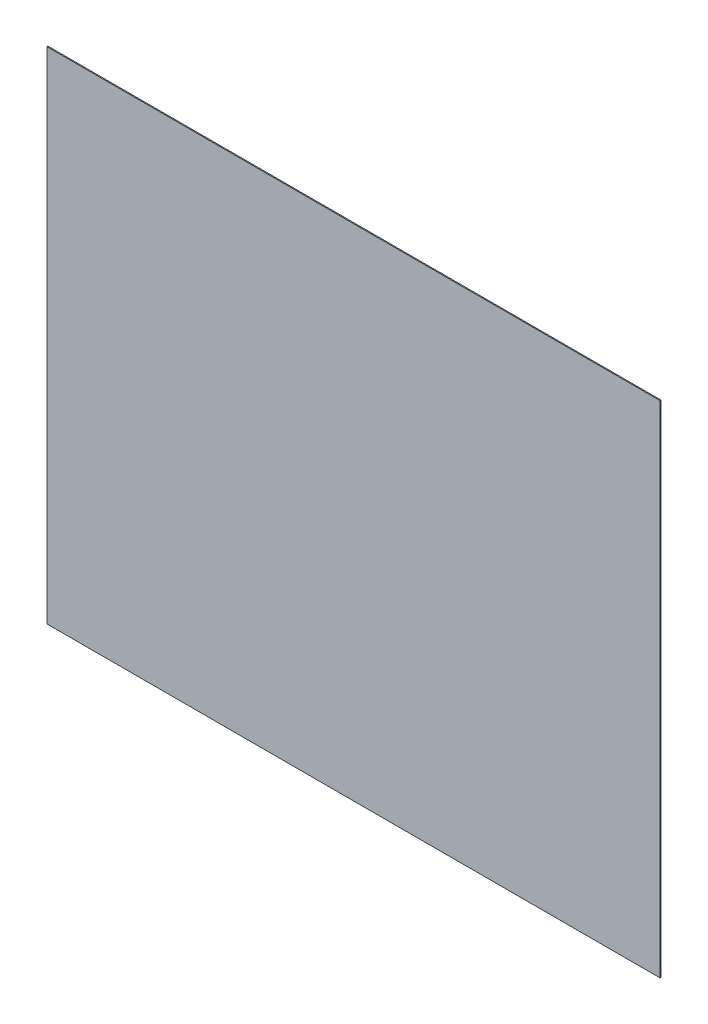
SolidWorks part; units mm, degrees
material "Aleación 1060"
ref_plane "Alzado" through (0, 0, 0) normal (0, 0, 1) x (1, 0, 0)
ref_plane "Planta" through (0, 0, 0) normal (0, 1, 0) x (1, 0, 0)
ref_plane "Vista lateral" through (0, 0, 0) normal (1, 0, 0) x (0, 0, -1)
sketch "Croquis1" plane through (0, 0, 0) normal (0, 0, 1) x (1, 0, 0)
  line L1 (0, 0) -> (1730, 0)
  line L2 (0, 0) -> (0, 1410)
  line L3 (0, 1410) -> (1730, 1410)
  line L4 (1730, 0) -> (1730, 1410)
  dimension "D1" = 1410
  dimension "D2" = 1730
extrude "Saliente-Extruir1" add sketch "Croquis1" along normal blind 2.733
